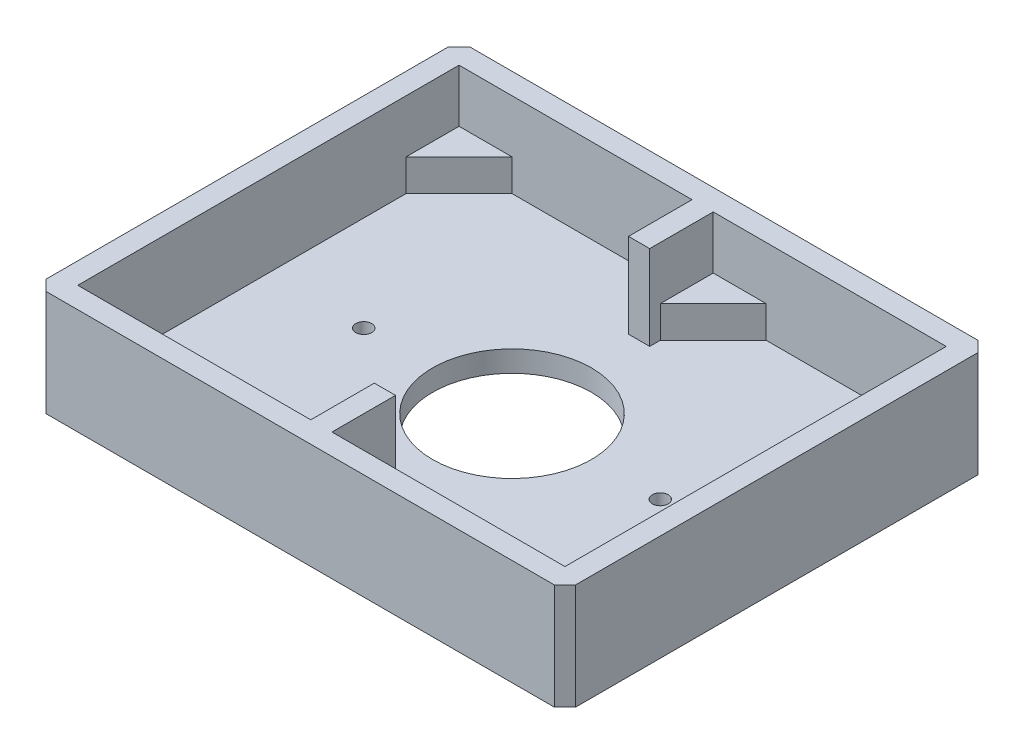
SolidWorks part; units mm, degrees
ref_plane "Front Plane" through (0, 0, 0) normal (0, 0, 1) x (1, 0, 0)
ref_plane "Top Plane" through (0, 0, 0) normal (0, 1, 0) x (1, 0, 0)
ref_plane "Right Plane" through (0, 0, 0) normal (1, 0, 0) x (0, 0, -1)
sketch "Sketch1" plane through (0, 0, 0) normal (0, 1, 0) x (1, 0, 0)
  line L1 (-50, 40) -> (50, 40)
  line L2 (-50, 40) -> (-50, -40)
  line L3 (-50, -40) -> (50, -40)
  line L4 (50, 40) -> (50, -40)
  line L5 (-50, 40) -> (50, -40) construction
  line L6 (-50, -40) -> (50, 40) construction
  point P0 (0, 0)
  dimension "D1" = 80
  dimension "D2" = 100
extrude "Boss-Extrude1" add sketch "Sketch1" against normal blind 20 contours L1 L4 L3 L2
shell "Shell2" thickness 4
sketch "Sketch14" plane through (0, 0, 0) normal (0, 1, 0) x (1, 0, 0)
  line L0 (0, 14.1004) -> (0, -14.1004) construction
  line L1 (-64.6346, 0) -> (64.6346, 0) construction
  line L3 (-2, -24) -> (2, -24)
  line L4 (-2, -24) -> (-2, -36)
  line L5 (-2, -36) -> (2, -36)
  line L12 (2, -24) -> (2, -36)
  line L13 (-46, -36) -> (46, -36) construction
  line L14 (-2, 24) -> (-2, 36)
  line L15 (-2, 24) -> (2, 24)
  line L16 (2, 24) -> (2, 36)
  line L17 (-2, 36) -> (2, 36)
  point P4 (0, 0)
  point P8 (0, 0)
  dimension "D1" = 12
  dimension "D2" = 4
extrude "Boss-Extrude5" add sketch "Sketch14" against normal up to surface (16 mm away) up to face at (0, -16, 0)
sketch "Sketch5" plane through (0, -16, 0) normal (0, 1, 0) x (1, 0, 0)
  circle A4 centre (0, 0) radius 15
  dimension "D1" = 30
extrude "Cut-Extrude1" cut sketch "Sketch5" against normal through all
sketch "Sketch15" plane through (0, -16, 0) normal (0, 1, 0) x (1, 0, 0)
  line L0 (-46, 36) -> (-46, 26)
  line L1 (-46, 36) -> (-46, -36) construction
  line L2 (-46, 26) -> (-36, 36)
  line L3 (-46, 36) -> (-2, 36) construction
  line L4 (-36, 36) -> (-46, 36)
  line L5 (-2, 36) -> (-2, 26)
  line L6 (-2, 26) -> (-12, 36)
  line L7 (-12, 36) -> (-2, 36)
  line L8 (-11, 0) -> (11, 0) construction
  line L9 (-2, -26) -> (-12, -36)
  line L10 (-2, -36) -> (-2, -26)
  line L11 (-12, -36) -> (-2, -36)
  line L12 (-46, -26) -> (-36, -36)
  line L13 (-46, -36) -> (-46, -26)
  line L14 (-36, -36) -> (-46, -36)
  line L15 (0, -11) -> (0, 11) construction
  line L16 (2, -36) -> (2, -26)
  line L17 (12, -36) -> (2, -36)
  line L18 (2, -26) -> (12, -36)
  line L19 (46, -36) -> (46, -26)
  line L20 (36, -36) -> (46, -36)
  line L21 (46, -26) -> (36, -36)
  line L22 (2, 26) -> (12, 36)
  line L23 (2, 36) -> (2, 26)
  line L24 (12, 36) -> (2, 36)
  line L25 (46, 26) -> (36, 36)
  line L26 (46, 36) -> (46, 26)
  line L27 (36, 36) -> (46, 36)
  dimension "D1" = 10
  dimension "D2" = 10
  dimension "D3" = 10
  dimension "D4" = 10
extrude "Boss-Extrude6" add sketch "Sketch15" along normal blind 6
chamfer "Chamfer1" distance 2 angle 45 4 edges at (-50, -10, 40) (50, -10, 40) (50, -10, -40) (-50, -10, -40)
sketch "Sketch16" plane through (0, -16, 0) normal (0, 1, 0) x (1, 0, 0)
  line L0 (0, 0) -> (0, -50000) construction
  circle A0 centre (-28, 0) radius 1.5
  circle A1 centre (28, 0) radius 1.5
  dimension "D1" = 56
  dimension "D2" = 3
extrude "Cut-Extrude2" cut sketch "Sketch16" against normal up to surface (4 mm away) up to face at (0, -20, 15)
